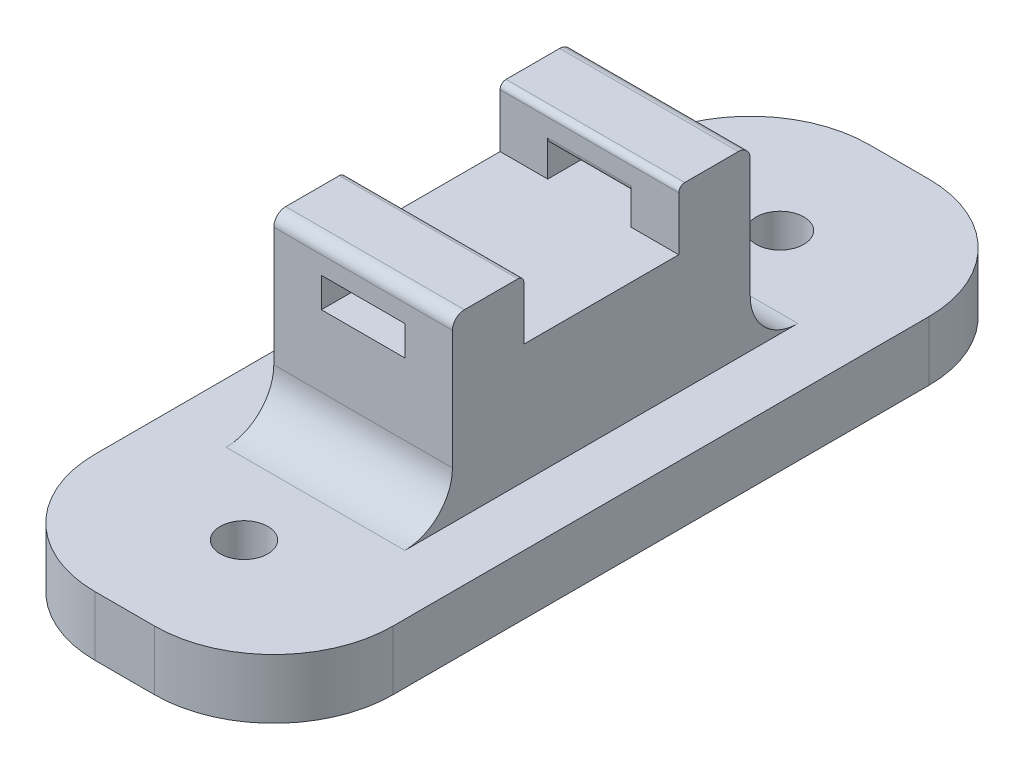
SolidWorks part; units mm, degrees
ref_plane "Front Plane" through (0, 0, 0) normal (0, 0, 1) x (1, 0, 0)
ref_plane "Top Plane" through (0, 0, 0) normal (0, 1, 0) x (1, 0, 0)
ref_plane "Right Plane" through (0, 0, 0) normal (1, 0, 0) x (0, 0, -1)
sketch "Sketch1" plane through (0, 0, 0) normal (0, 1, 0) x (1, 0, 0)
  line L1 (0, 0) -> (25, 0)
  line L2 (0, 0) -> (0, 65)
  line L3 (0, 65) -> (25, 65)
  line L4 (25, 0) -> (25, 65)
  dimension "D1" = 65
  dimension "D2" = 25
extrude "Boss-Extrude1" add sketch "Sketch1" along normal blind 5
sketch "Sketch2" plane through (0, 0, 0) normal (0, 1, 0) x (1, 0, 0)
  line L0 (12.5, 65) -> (12.5, 0) construction
  line L1 (25, 65) -> (0, 65) construction
  line L2 (0, 0) -> (25, 0) construction
  circle A0 centre (12.5, 55) radius 2
  circle A1 centre (12.5, 10) radius 2
  dimension "D1" = 4
  dimension "D2" = 45
  dimension "D3" = 10
extrude "Cut-Extrude1" cut sketch "Sketch2" along normal through all
sketch "Sketch3" plane through (0, 5, 0) normal (0, 1, 0) x (1, 0, 0)
  line L0 (12.5, 0) -> (12.5, 65) construction
  line L1 (20, 20) -> (5, 20)
  line L2 (20, 20) -> (20, 45)
  line L3 (20, 45) -> (5, 45)
  line L4 (5, 20) -> (5, 45)
  line L5 (0, 0) -> (25, 0) construction
  line L6 (25, 65) -> (0, 65) construction
  line L7 (12.5, 20) -> (12.5, 45) construction
  dimension "D1" = 25
  dimension "D2" = 15
  dimension "D3" = 20
extrude "Boss-Extrude2" add sketch "Sketch3" along normal blind 10
sketch "Sketch4" plane through (0, 15, 0) normal (0, 1, 0) x (1, 0, 0)
  line L0 (20, 20) -> (20, 45) construction
  line L1 (5, 45) -> (20, 45)
  line L2 (5, 45) -> (5, 39)
  line L3 (5, 39) -> (20, 39)
  line L4 (20, 45) -> (20, 39)
  line L5 (5, 45) -> (5, 20) construction
  line L6 (20, 20) -> (5, 20)
  line L7 (20, 20) -> (20, 26)
  line L8 (20, 26) -> (5, 26)
  line L9 (5, 20) -> (5, 26)
  dimension "D1" = 6
  dimension "D2" = 6
extrude "Boss-Extrude3" add sketch "Sketch4" along normal blind 5
sketch "Sketch5" plane through (0, 0, -45) normal (0, 0, -1) x (-1, 0, 0)
  line L1 (-16, 17.5) -> (-9, 17.5)
  line L2 (-16, 17.5) -> (-16, 15)
  line L3 (-16, 15) -> (-9, 15)
  line L4 (-9, 17.5) -> (-9, 15)
  line L5 (-5, 20) -> (-5, 5) construction
  line L6 (-20, 5) -> (-5, 5) construction
  dimension "D1" = 7
  dimension "D2" = 2.5
  dimension "D3" = 10
  dimension "D4" = 4
extrude "Cut-Extrude2" cut sketch "Sketch5" against normal through all
fillet "Fillet1" radius 0.5 2 edges at (12.5, 20, -39) (12.5, 17.5, -39)
fillet "Fillet2" radius 0.5 2 edges at (12.5, 20, -26) (12.5, 17.5, -26)
fillet "Fillet3" radius 1 2 edges at (12.5, 20, -20) (12.5, 20, -45)
fillet "Fillet4" radius 10 4 edges at (25, 2.5, 0) (0, 2.5, 0) (0, 2.5, -65) (25, 2.5, -65)
fillet "Fillet5" radius 4 2 edges at (12.5, 5, -45) (12.5, 5, -20)
